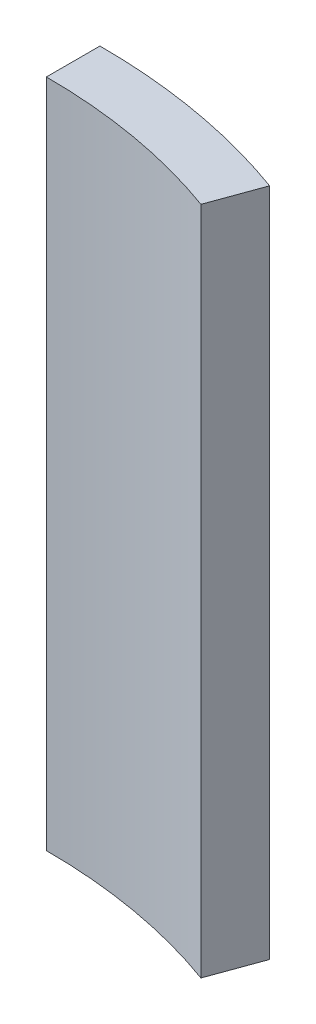
SolidWorks part; units mm, degrees
material "Molybdenum"
ref_plane "Front Plane" through (0, 0, 0) normal (0, 0, 1) x (1, 0, 0)
ref_plane "Top Plane" through (0, 0, 0) normal (0, 1, 0) x (1, 0, 0)
ref_plane "Right Plane" through (0, 0, 0) normal (1, 0, 0) x (0, 0, -1)
sketch "Sketch1" plane through (0, 0, 0) normal (0, 1, 0) x (1, 0, 0)
  line L0 (0, -55) -> (0, 55) construction
  line L1 (0, 0) -> (7.6829, 21.1476) construction
  line L2 (7, 19.2678) -> (7.6829, 21.1476)
  line L3 (0, 20.5) -> (0, 22.5)
  arc A0 (0, 22.5) -> (7.6829, 21.1476) centre (0, 0) cw
  arc A1 (0, 20.5) -> (7, 19.2678) centre (0, 0) cw
  dimension "D1" = 22.5
  dimension "D2" = 20.5
  dimension "D3" = 7
extrude "Boss-Extrude1" add sketch "Sketch1" along normal blind 25
